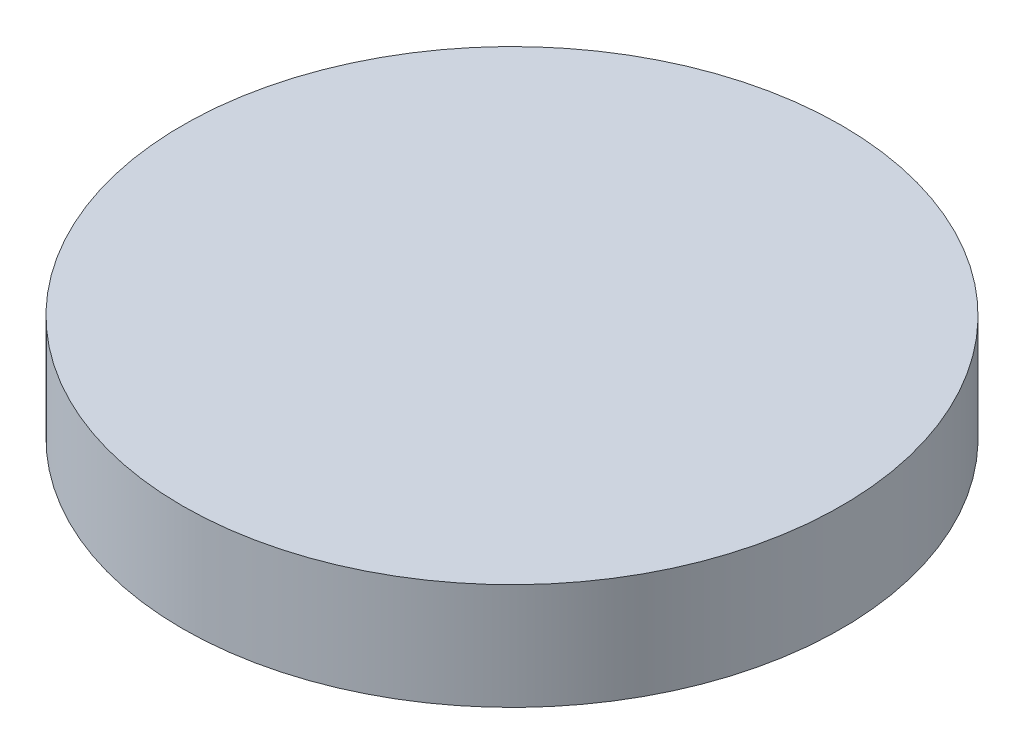
SolidWorks part; units mm, degrees
ref_plane "Front Plane" through (0, 0, 0) normal (0, 0, 1) x (1, 0, 0)
ref_plane "Top Plane" through (0, 0, 0) normal (0, 1, 0) x (1, 0, 0)
ref_plane "Right Plane" through (0, 0, 0) normal (1, 0, 0) x (0, 0, -1)
sketch "Sketch2" plane through (0, 0, 0) normal (0, 1, 0) x (1, 0, 0)
  circle A0 centre (0, 0) radius 77.5
  circle A1 centre (0, 0) radius 72.5
  circle A2 centre (0, 0) radius 52.5
  circle A3 centre (0, 0) radius 47.5
  dimension "D1" = 155
  dimension "D2" = 5
  dimension "D3" = 20
  dimension "D4" = 5
extrude "Boss-Extrude1" add sketch "Sketch2" along normal blind 20 contours A2 A3 | A0 A1
sketch "Sketch3" plane through (0, 20, 0) normal (0, 1, 0) x (1, 0, 0)
  circle A0 centre (0, 0) radius 77.5
  dimension "D1" = 155
extrude "Boss-Extrude2" add sketch "Sketch3" along normal blind 5
